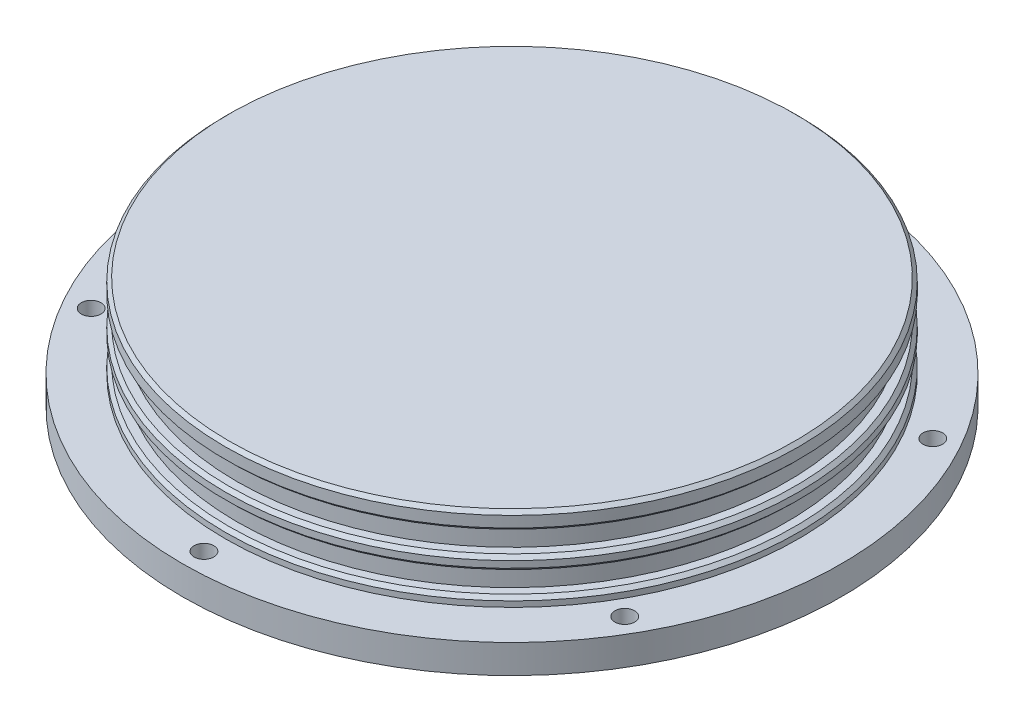
SolidWorks part; units mm, degrees
material "Glass"
ref_plane "Front Plane" through (0, 0, 0) normal (0, 0, 1) x (1, 0, 0)
ref_plane "Top Plane" through (0, 0, 0) normal (0, 1, 0) x (1, 0, 0)
ref_plane "Right Plane" through (0, 0, 0) normal (1, 0, 0) x (0, 0, -1)
sketch "Sketch1" plane through (0, 0, 0) normal (0, 1, 0) x (1, 0, 0)
  circle A0 centre (0, 0) radius 36.5125
extrude "Extrude1" add sketch "Sketch1" along normal blind 3.175
sketch "Sketch2" plane through (0, 3.175, 0) normal (0, 1, 0) x (-1, 0, 0)
  circle A0 centre (0, 0) radius 31.75
extrude "Extrude2" add sketch "Sketch2" along normal blind 9.2075
sketch "Sketch4" plane through (0, 0, 0) normal (1, 0, 0) x (0, 0, -1)
  line L0 (-31.75, 12.3825) -> (-31.75, 3.175) construction
  line L1 (-31.75, 10.4051) -> (-30.48, 10.4051)
  line L2 (-31.75, 10.4051) -> (-31.75, 8.0429)
  line L3 (-31.75, 8.0429) -> (-30.48, 8.0429)
  line L4 (-30.48, 10.4051) -> (-30.48, 8.0429)
  line L5 (0, 0) -> (0, 13.8799) construction
  line L6 (-31.75, 6.5416) -> (-30.48, 6.5416)
  line L7 (-31.75, 6.5416) -> (-31.75, 4.1794)
  line L8 (-31.75, 4.1794) -> (-30.48, 4.1794)
  line L9 (-30.48, 6.5416) -> (-30.48, 4.1794)
  line L10 (-36.5125, 0) -> (36.5125, 0) construction
  dimension "D1" = 2.3622
  dimension "D2" = 2.3622
  dimension "D3" = 30.48
revolve "Cut-Revolve7" cut sketch "Sketch4" angle 360 about L5
sketch "Sketch6" plane through (0, 0, 0) normal (0, -1, 0) x (1, 0, 0)
  line L0 (0, 0) -> (0, 36.5125) construction
  line L1 (0, 0) -> (0, -36.5125) construction
  line L2 (0, 0) -> (31.6208, 18.2563) construction
  line L3 (0, 0) -> (31.6208, -18.2562) construction
  line L4 (0, 0) -> (-31.6208, -18.2563) construction
  line L5 (0, 0) -> (-31.6208, 18.2562) construction
  circle A0 centre (0, 0) radius 36.5125 construction
chamfer "Chamfer1" distance 0.381 angle 45 5 edges at (0, 12.3825, 31.75) (0, 4.1794, -31.75) (0, 6.5416, -31.75) (0, 8.0429, -31.75) (0, 10.4051, -31.75)
hole_wizard "#2-56 Tapped Hole1" positions "3DSketch1" profile "Sketch5" tap size "#2-56" standard "Ansi Inch"
sketch3d "3DSketch1"
  point P0 (-29.5585, 0, 17.0656)
  point P2 (0, 0, 34.1313)
  point P4 (29.5585, 0, 17.0656)
  point P6 (29.5585, 0, -17.0656)
  point P8 (0, 0, -34.1313)
  point P10 (-29.5585, 0, -17.0656)
  point P34 (0, 0, 0)
  dimension "D1" = 34.1313
  dimension "D2" = 34.1313
  dimension "D6" = 34.1313
  dimension "D3" = 34.1313
  dimension "D4" = 34.1313
  dimension "D5" = 34.1313
  dimension "D8" = 34.1313
  dimension "D7" = 34.1313
  dimension "D9" = 34.1313
  dimension "D10" = 34.1313
  dimension "D11" = 34.1313
  dimension "D12" = 34.1313
sketch "Sketch5" plane through (-29.5585, 0, 17.0656) normal (1, 0, 0) x (0, 0, -1)
  line L0 (0, 0) -> (0, 6.1222)
  line L1 (0, 6.1222) -> (0.889, 5.588)
  line L2 (0.889, 5.588) -> (0.889, 4.318)
  line L3 (0.889, 4.318) -> (1.0922, 4.318)
  line L4 (1.0922, 4.318) -> (1.0922, 0)
  line L5 (1.0922, 0) -> (0, 0)
  line L10 (0, 6.1222) -> (-0.889, 5.588) construction
  line L11 (0, -6.35) -> (0, 107.95) construction
  dimension "Tap Drill Dia." = 1.778
  dimension "Tap Drill Depth" = 5.588
  dimension "Thread Major Dia." = 2.1844
  dimension "Thread Depth" = 4.318
  dimension "Drill Angle" = 118
sketch "Sketch7" plane through (0, 12.3825, 0) normal (0, 1, 0) x (-1, 0, 0)
  line L0 (0, 0) -> (0, 38.4938) construction
